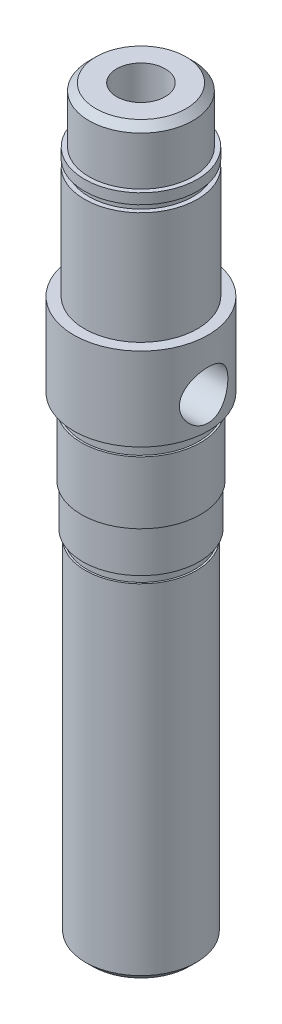
SolidWorks part; units mm, degrees
ref_plane "Plan de face" through (0, 0, 0) normal (0, 0, 1) x (1, 0, 0)
ref_plane "Plan de dessus" through (0, 0, 0) normal (0, 1, 0) x (1, 0, 0)
ref_plane "Plan de droite" through (0, 0, 0) normal (1, 0, 0) x (0, 0, -1)
sketch "Esquisse1" plane through (0, 0, 0) normal (0, 0, 1) x (1, 0, 0)
  line L0 (0, 0) -> (-7, 0)
  line L2 (-7, 0) -> (-8, 1)
  line L4 (-8, 1) -> (-8, 50)
  line L6 (-8, 50) -> (-7.75, 50)
  line L7 (-7.75, 50) -> (-7.75, 51.3)
  line L9 (-7.75, 51.3) -> (-8.4, 51.3)
  line L10 (-8.4, 51.3) -> (-8.4, 57.3)
  line L12 (-8.4, 57.3) -> (-8.6, 57.3)
  line L13 (-8.6, 57.3) -> (-8.6, 66.3)
  line L15 (-8.6, 66.3) -> (-8.33, 66.3)
  line L16 (-8.33, 66.3) -> (-8.33, 68.3)
  line L18 (-8.33, 68.3) -> (-9.7, 68.3)
  line L22 (-9.7, 80.3) -> (-8.15, 80.3)
  line L23 (-8.15, 80.3) -> (-8.15, 96.5)
  line L24 (-8.15, 96.5) -> (-7.5, 96.5)
  line L26 (-7.5, 96.5) -> (-7.5, 97.5)
  line L28 (-7.5, 97.5) -> (-8.15, 97.5)
  line L29 (-8.15, 97.5) -> (-8.15, 99)
  line L31 (-8.15, 99) -> (-7.5, 99)
  line L32 (-7.5, 99) -> (-7.5, 106)
  line L33 (-7.5, 106) -> (-6.5, 107)
  line L35 (-6.5, 107) -> (0, 107)
  line L36 (0, 107) -> (0, 0)
  line L37 (-9.7, 80.3) -> (-9.7, 68.3)
  dimension "D1" = 7
  dimension "D2" = 1
  dimension "D3" = 1
  dimension "D4" = 49
  dimension "D5" = 0.25
  dimension "D6" = 1.3
  dimension "D7" = 0.65
  dimension "D8" = 6
  dimension "D9" = 0.2
  dimension "D10" = 8.6
  dimension "D11" = 0.27
  dimension "D12" = 0.65
  dimension "D13" = 1
  dimension "D14" = 1
  dimension "D15" = 7.5
  dimension "D16" = 0.65
  dimension "D17" = 0.65
  dimension "D18" = 1.37
revolve "Révolution1" add sketch "Esquisse1" angle 360 about L36
sketch "Esquisse2" plane through (0, 0, 0) normal (0, 0, 1) x (1, 0, 0)
  line L0 (-7, 0) -> (7, 0) construction
  line L1 (0, 47.1) -> (0, 0) construction
  line L8 (5.8095, 2.7) -> (5.8095, 47.1)
  line L9 (5.8095, 47.1) -> (-5.8095, 47.1)
  line L10 (-5.8095, 47.1) -> (-5.8095, 2.7)
  line L11 (-5.8095, 2.7) -> (5.8095, 2.7)
  dimension "D1" = 11.619
  dimension "D2" = 44.4
  dimension "D3" = 2.7
extrude "Enlèv. mat.-Extru.1" cut sketch "Esquisse2" against normal through all from offset 5.5 offset against normal yes
sketch "Esquisse5" plane through (0, 0, 0) normal (1, 0, 0) x (0, 0, -1)
  arc A2 (0, 76.3) -> (0, 69.3) centre (0, 72.8) ccw
  arc A3 (0, 69.3) -> (0, 76.3) centre (0, 72.8) ccw
extrude "Enlèv. mat.-Extru.2" cut sketch "Esquisse5" along normal through all
sketch "Esquisse6" plane through (0, 0, 0) normal (0, -1, 0) x (1, 0, 0)
  circle A0 centre (0, 0) radius 3.5
  circle A1 centre (0, 0) radius 7
  circle A2 centre (0, 0) radius 7 construction
  dimension "D2" = 7
  dimension "D1" = 0
extrude "Enlèv. mat.-Extru.3" cut sketch "Esquisse6" against normal blind 120
chamfer "Chanfrein1" distance 1 angle 45 1 edges at (0, 0, -3.5)
